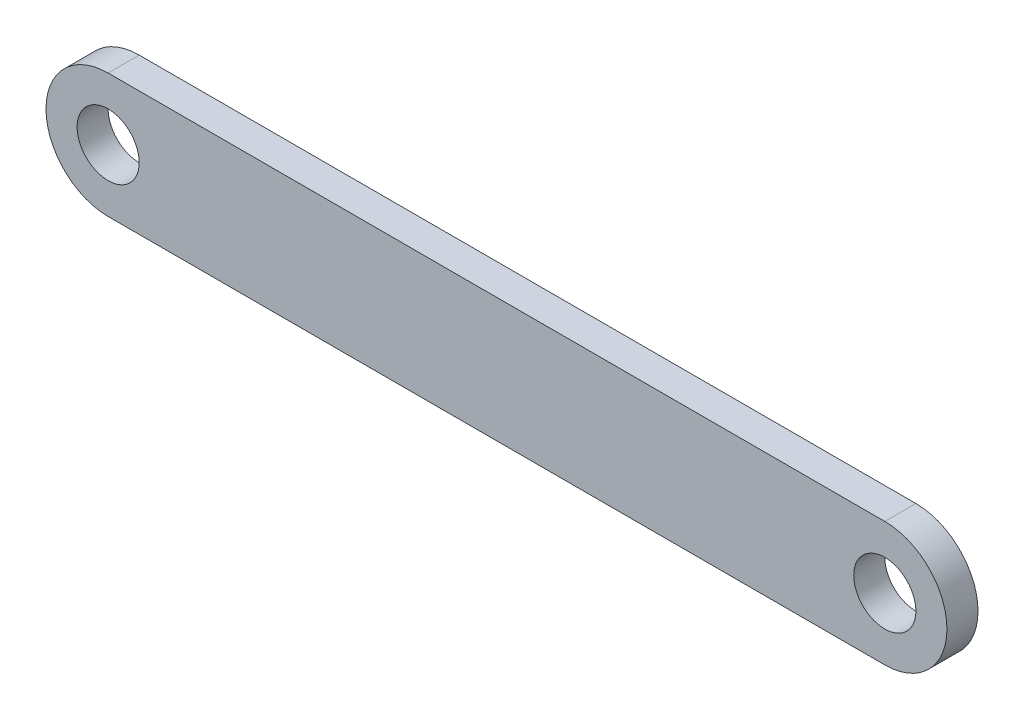
SolidWorks part; units mm, degrees
ref_plane "Front Plane" through (0, 0, 0) normal (0, 0, 1) x (1, 0, 0)
ref_plane "Top Plane" through (0, 0, 0) normal (0, 1, 0) x (1, 0, 0)
ref_plane "Right Plane" through (0, 0, 0) normal (1, 0, 0) x (0, 0, -1)
sketch "Sketch2" plane through (0, 0, 0) normal (0, 0, 1) x (1, 0, 0)
  line L0 (0, 0) -> (-50, 0) construction
  line L1 (0, -4) -> (-50, -4)
  line L2 (0, 4) -> (-50, 4)
  line L3 (0, 0) -> (23.9987, 0) construction
  line L4 (23.9987, 0) -> (0, 0) construction
  line L5 (0, 0) -> (0, 13.0117) construction
  line L6 (0, 13.0117) -> (0, -16.6739) construction
  line L7 (-25, 0) -> (-25, 25.2508) construction
  line L8 (-25, 25.2508) -> (-25, -21.0143) construction
  arc A0 (0, -4) -> (0, 4) centre (0, 0) ccw
  arc A1 (-50, 4) -> (-50, -4) centre (-50, 0) ccw
  circle A2 centre (-50, 0) radius 2
  circle A3 centre (0, 0) radius 2
  point P3 (-25, 0)
  dimension "D3" = 4
  dimension "D1" = 8
  dimension "D2" = 50
extrude "Boss-Extrude1" add sketch "Sketch2" along normal blind 2
